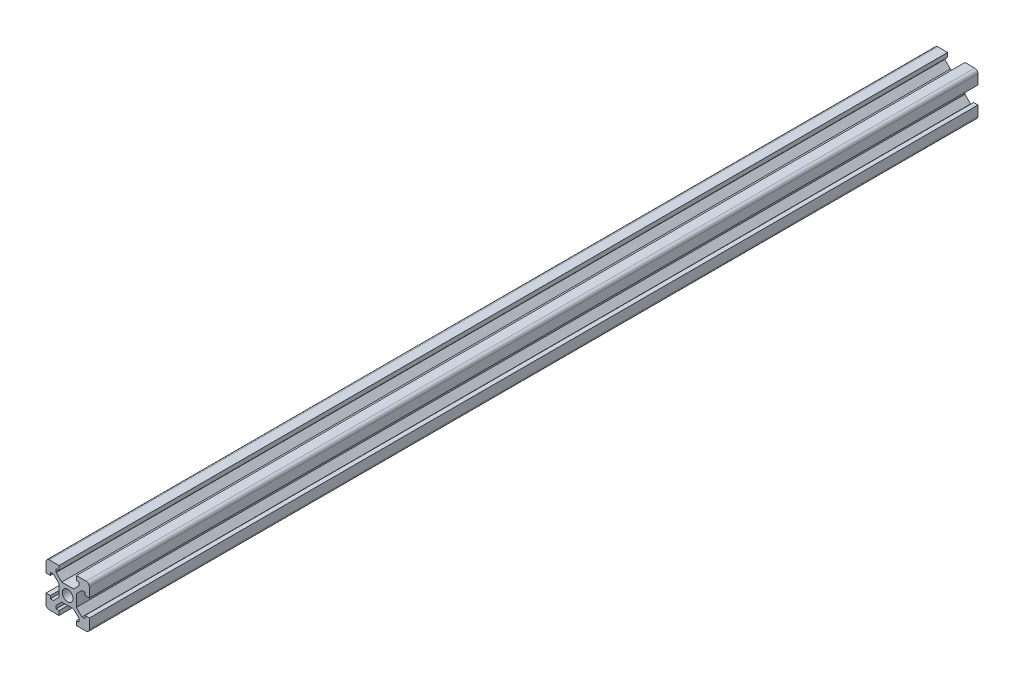
SolidWorks part; units mm, degrees
material "1060 Сплав"
ref_plane "Top" through (0, 0, 0) normal (0, 0, 1) x (1, 0, 0)
ref_plane "Сверху" through (0, 0, 0) normal (0, 1, 0) x (1, 0, 0)
ref_plane "Справа" through (0, 0, 0) normal (1, 0, 0) x (0, 0, -1)
sketch "Эскиз1" plane through (0, 0, 0) normal (0, 0, 1) x (1, 0, 0)
  line L0 (14, 20) -> (20, 20)
  line L1 (0, 0) -> (6, 0)
  line L2 (0, 0) -> (0, 6)
  line L3 (0, 20) -> (6, 20)
  line L4 (20, 0) -> (20, 6)
  line L5 (0, 14) -> (0, 20)
  line L6 (14, 0) -> (20, 0)
  line L7 (20, 14) -> (20, 20)
  line L8 (0, 0) -> (35355.3391, 35355.3391) construction
  line L9 (0, 20) -> (35355.3391, -35335.3391) construction
  line L22 (0, 14) -> (2, 14)
  line L23 (2, 14) -> (2, 15.3)
  line L24 (2, 15.3) -> (3.4272, 15.3)
  line L25 (3.4272, 15.3) -> (6, 12.7272)
  line L26 (6, 12.7272) -> (6, 7.2728)
  line L27 (6, 7.2728) -> (3.4272, 4.7)
  line L28 (3.4272, 4.7) -> (2, 4.7)
  line L29 (2, 4.7) -> (2, 6)
  line L30 (2, 6) -> (0, 6)
  line L31 (6, 0) -> (6, 2)
  line L32 (6, 2) -> (4.7, 2)
  line L33 (4.7, 2) -> (4.7, 3.4272)
  line L34 (4.7, 3.4272) -> (7.2728, 6)
  line L35 (7.2728, 6) -> (12.684, 6)
  line L36 (12.684, 6) -> (15.3, 3.4272)
  line L37 (15.3, 3.4272) -> (15.3, 2)
  line L38 (15.3, 2) -> (14, 2)
  line L39 (14, 2) -> (14, 0)
  line L40 (20, 6) -> (18, 6)
  line L41 (18, 6) -> (18, 4.7)
  line L42 (18, 4.7) -> (16.5728, 4.7)
  line L43 (16.5728, 4.7) -> (14, 7.2728)
  line L44 (14, 7.2728) -> (14, 12.7272)
  line L45 (14, 12.7272) -> (16.5728, 15.3)
  line L46 (16.5728, 15.3) -> (18, 15.3)
  line L47 (18, 15.3) -> (18, 14)
  line L48 (18, 14) -> (20, 14)
  line L49 (6, 20) -> (6, 18)
  line L50 (6, 18) -> (4.7, 18)
  line L51 (4.7, 18) -> (4.7, 16.5728)
  line L52 (4.7, 16.5728) -> (7.2728, 14)
  line L53 (7.2728, 14) -> (12.7272, 14)
  line L54 (12.7272, 14) -> (15.3, 16.5728)
  line L55 (15.3, 16.5728) -> (15.3, 18)
  line L56 (15.3, 18) -> (14, 18)
  line L57 (14, 18) -> (14, 20)
  circle A0 centre (10, 10) radius 2.5
extrude "Бобышка-Вытянуть1" add sketch "Эскиз1" along normal blind 410
fillet "Скругление1" radius 1.5 4 edges at (0, 20, 205) (20, 20, 205) (20, 0, 205) (0, 0, 205)
